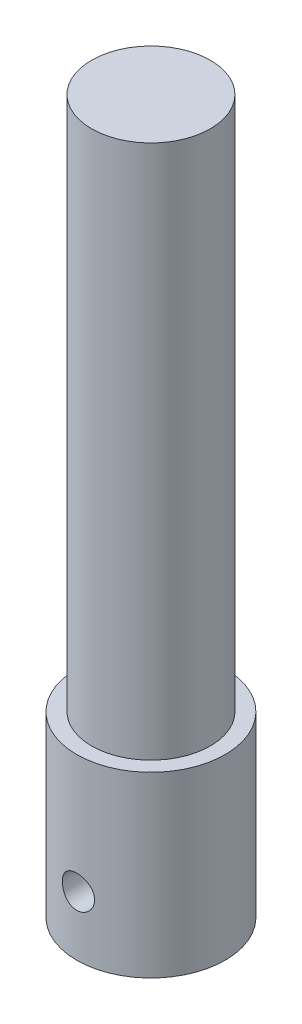
SolidWorks part; units mm, degrees
ref_plane "Front" through (0, 0, 0) normal (0, 0, 1) x (1, 0, 0)
ref_plane "Top" through (0, 0, 0) normal (0, 1, 0) x (1, 0, 0)
ref_plane "Right" through (0, 0, 0) normal (1, 0, 0) x (0, 0, -1)
sketch "Sketch1" plane through (0, 0, 0) normal (0, 1, 0) x (1, 0, 0)
  circle A0 centre (0, 0) radius 7.9375
  dimension "D1" = 15.875
extrude "Boss-Extrude1" add sketch "Sketch1" along normal blind 76.2 contours A0
hole_wizard "M6x1.0 Tapped Hole1" positions "Sketch6" profile "Sketch7" tap size "M6x1.0" standard "ANSI Metric"
sketch "Sketch6" plane through (0, 0, 0) normal (0, -1, 0) x (-1, 0, 0)
  point P0 (0, 0)
sketch "Sketch7" plane through (0, 0, 0) normal (1, 0, 0) x (0, 0, -1)
  line L0 (0, 0) -> (0, 31.5021)
  line L1 (0, 31.5021) -> (2.5, 30)
  line L2 (2.5, 30) -> (2.5, 0)
  line L5 (2.5, 0) -> (0, 0)
  line L10 (0, 31.5021) -> (-2.5, 30) construction
  line L11 (0, -6.35) -> (0, 107.95) construction
  dimension "Tap Drill Dia." = 5
  dimension "Tap Drill Depth" = 30
  dimension "Drill Angle" = 118
cosmetic thread "Hole Thread1" parameters "D1"=23, "D2"=6
hole_wizard "Ø10.0 (10) Diameter Hole2" positions "Sketch8" profile "Sketch9" hole size "Ø10.0" standard "ANSI Metric"
sketch "Sketch8" plane through (0, 0, 0) normal (0, -1, 0) x (-1, 0, 0)
  point P0 (0, 0)
sketch "Sketch9" plane through (0, 0, 0) normal (1, 0, 0) x (0, 0, -1)
  line L0 (0, 0) -> (0, 17.0043)
  line L1 (0, 17.0043) -> (5, 14)
  line L2 (5, 14) -> (5, 0)
  line L5 (5, 0) -> (0, 0)
  line L10 (0, 17.0043) -> (-5, 14) construction
  line L11 (0, -6.35) -> (0, 107.95) construction
  dimension "Hole Dia." = 10
  dimension "Hole Depth" = 14
  dimension "Drill Angle" = 118
ref_plane "Plane1" through (0, 0, 7.9375) normal (0, 0, 1) x (1, 0, 0)
hole_wizard "#8-32 Tapped Hole1" positions "Sketch10" profile "Sketch12" tap size "#8-32" standard "ANSI Inch" end condition through all
sketch "Sketch10" plane through (0, 0, 7.9375) normal (0, 0, 1) x (1, 0, 0)
  point P0 (0, 6.35)
  dimension "D1" = 6.35
sketch "Sketch12" plane through (0, 6.35, 7.9375) normal (1, 0, 0) x (0, -1, 0)
  line L0 (0, 0) -> (0, 15.875)
  line L1 (0, 15.875) -> (1.7272, 15.875)
  line L2 (1.7272, 15.875) -> (1.7272, 0)
  line L5 (1.7272, 0) -> (0, 0)
  line L11 (0, -6.35) -> (0, 107.95) construction
  dimension "Thru Tap Drill Dia." = 3.4544
  dimension "Thru Tap Drill Depth" = 15.875
cosmetic thread "Hole Thread2" parameters "D2"=4.1656
sketch "Sketch15" plane through (0, 76.2, 0) normal (0, 1, 0) x (1, 0, 0)
  circle A0 centre (0, 0) radius 6.35
  circle A1 centre (0, 0) radius 7.9375 construction
  circle A2 centre (0, 0) radius 7.9375
  dimension "D1" = 12.7
extrude "Cut-Extrude2" cut sketch "Sketch15" against normal offset from surface (57.15 mm away) 19.05 up to face at (0, 0, -5)
